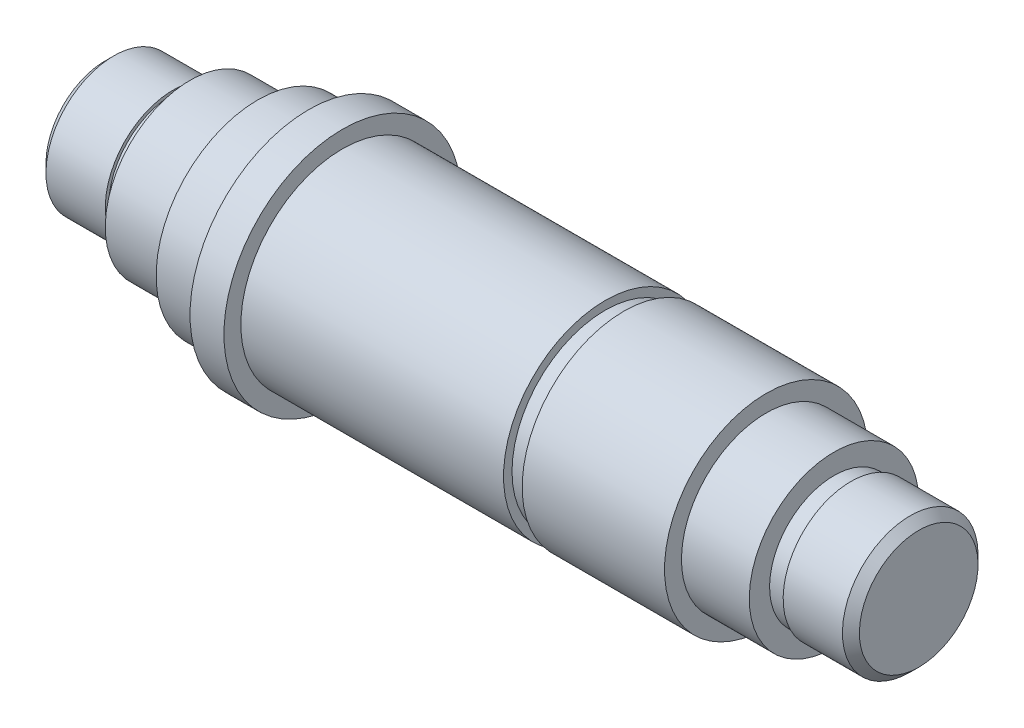
SolidWorks part; units mm, degrees
material "6061 合金"
ref_plane "前视基准面" through (0, 0, 0) normal (0, 0, 1) x (1, 0, 0)
ref_plane "上视基准面" through (0, 0, 0) normal (0, 1, 0) x (1, 0, 0)
ref_plane "右视基准面" through (0, 0, 0) normal (1, 0, 0) x (0, 0, -1)
sketch "草图1" plane through (0, 0, 0) normal (0, 0, 1) x (1, 0, 0)
  line L0 (-10.7644, 0) -> (37.2356, 0)
  line L3 (-10.7644, 3.5) -> (-10.7644, 0)
  line L4 (13.2356, 13.4841) -> (13.2356, -15.056) construction
  line L11 (37.2356, 3.5) -> (37.2356, 0)
  line L14 (-10.2644, 4) -> (-6.7644, 4)
  line L15 (-5.7644, 3.95) -> (-5.7644, 5)
  line L17 (32.2356, 5) -> (32.2356, 3.95)
  line L18 (33.2356, 4) -> (36.7356, 4)
  line L19 (-5.7644, 5) -> (-1.7644, 5)
  line L20 (-1.7644, 5) -> (-1.7644, 6)
  line L22 (28.2356, 6) -> (28.2356, 5)
  line L23 (28.2356, 5) -> (32.2356, 5)
  line L24 (-1.7644, 6) -> (1.2356, 6)
  line L25 (1.2356, 6) -> (1.2356, 7)
  line L26 (1.2356, 7) -> (3.2356, 7)
  line L27 (3.2356, 7) -> (3.2356, 6)
  line L28 (3.2356, 6) -> (18.7356, 6)
  line L29 (18.7356, 6) -> (18.7356, 5.5)
  line L30 (18.7356, 5.5) -> (19.8356, 5.5)
  line L31 (19.8356, 5.5) -> (19.8356, 6)
  line L32 (19.8356, 6) -> (28.2356, 6)
  line L33 (-5.7644, 3.95) -> (-5.7644, 3.8)
  line L34 (-5.7644, 3.8) -> (-6.7644, 3.8)
  line L35 (-6.7644, 3.8) -> (-6.7644, 4)
  line L36 (32.2356, 3.95) -> (32.2356, 3.8)
  line L37 (32.2356, 3.8) -> (33.2356, 3.8)
  line L38 (33.2356, 3.8) -> (33.2356, 4)
  line L39 (-10.7644, 3.5) -> (-10.2644, 4)
  line L40 (36.7356, 4) -> (37.2356, 3.5)
  point P3 (-10.7644, 4)
  point P4 (37.2356, 4)
  point P21 (3.2356, 6.5)
  dimension "D1" = 4
  dimension "D2" = 48
  dimension "D3" = 38
  dimension "D4" = 30
  dimension "D5" = 5
  dimension "D6" = 2
  dimension "D7" = 7
  dimension "D8" = 6
  dimension "D9" = 9
  dimension "D10" = 1.1
  dimension "D11" = 5.5
  dimension "D12" = 15.5
  dimension "D13" = 1
  dimension "D14" = 0.2
  dimension "D15" = 1
  dimension "D16" = 0.2
revolve "旋转1" add sketch "草图1" angle 360 about L0
